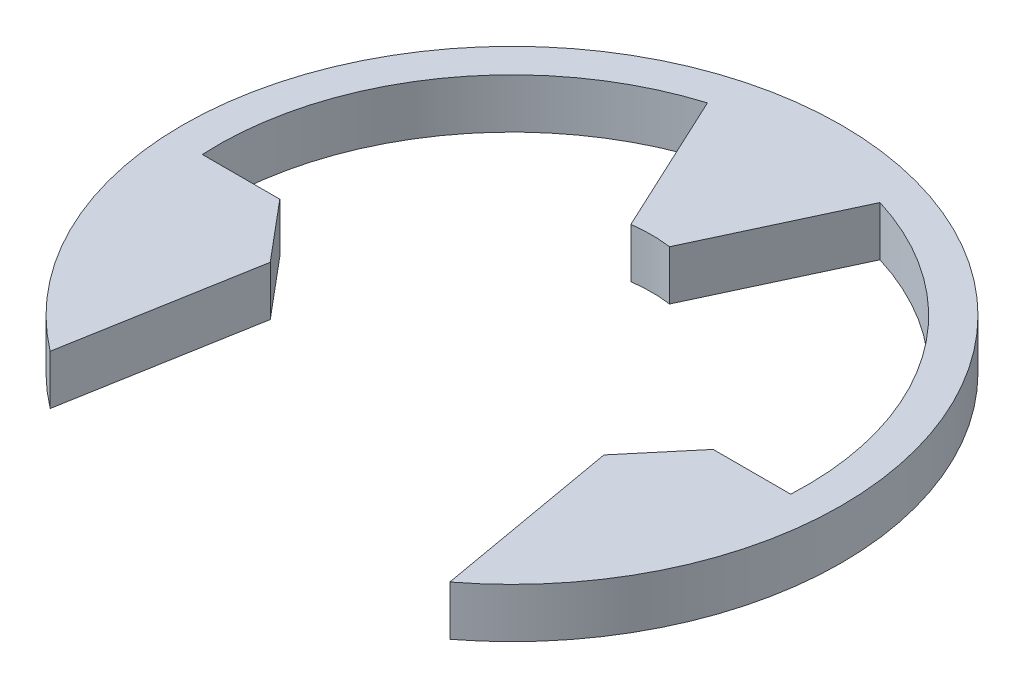
SolidWorks part; units mm, degrees
ref_plane "Front Plane" through (0, 0, 0) normal (0, 0, 1) x (1, 0, 0)
ref_plane "Top Plane" through (0, 0, 0) normal (0, 1, 0) x (1, 0, 0)
ref_plane "Right Plane" through (0, 0, 0) normal (1, 0, 0) x (0, 0, -1)
sketch "Sketch1" plane through (0, 0, 0) normal (0, 1, 0) x (1, 0, 0)
  line L0 (0, 3) -> (0, 2) construction
  line L1 (-0.2495, 1.7826) -> (-1.1126, 3.6335)
  line L2 (0.2495, 1.7826) -> (1.1126, 3.6335)
  line L9 (-2.5768, -3.3753) -> (-2.5775, -3.3792)
  line L10 (2.5759, -3.3707) -> (2.5775, -3.3792)
  line L11 (-4.25, 0) -> (4.25, 0) construction
  line L12 (-3.7947, -0.2) -> (-2.7947, -0.2)
  line L13 (-2.7947, -0.2) -> (-2.1519, -0.966)
  line L14 (-2.1519, -0.966) -> (-2.5775, -3.3792)
  line L15 (2.1519, -0.966) -> (2.7947, -0.2)
  line L16 (2.7947, -0.2) -> (3.7947, -0.2)
  line L17 (2.5759, -3.3707) -> (2.1519, -0.966)
  arc A0 (3.7947, -0.2) -> (3.6993, 0.869) centre (0, 0) ccw
  arc A1 (2.5775, -3.3792) -> (-2.5775, -3.3792) centre (0, 0) ccw
  arc A3 (-3.6993, 0.869) -> (-3.7947, -0.2) centre (0, 0) ccw
  arc A4 (-1.1126, 3.6335) -> (-3.6993, 0.869) centre (0, 0) ccw
  arc A5 (3.6993, 0.869) -> (1.1126, 3.6335) centre (0, 0) ccw
  arc A6 (0.2495, 1.7826) -> (-0.2495, 1.7826) centre (0, 0) ccw
  point P26 (0, 0)
  point P35 (0, 1.8)
  dimension "D1" = 7.6
  dimension "D2" = 8.5
  dimension "D4" = 25
  dimension "D5" = 2.45
  dimension "D7" = 130
  dimension "D10" = 130
  dimension "D3" = 2
  dimension "D6" = 0.2495
  dimension "D8" = 1
  dimension "D9" = 1
  dimension "D11" = 130
  dimension "D12" = 130
extrude "Boss-Extrude1" add sketch "Sketch1" along normal blind 0.64 contours A6 L2 A5 A0 L16 L15 L17 L10 A1 L9 L14 L13 L12 A3 A4 L1
